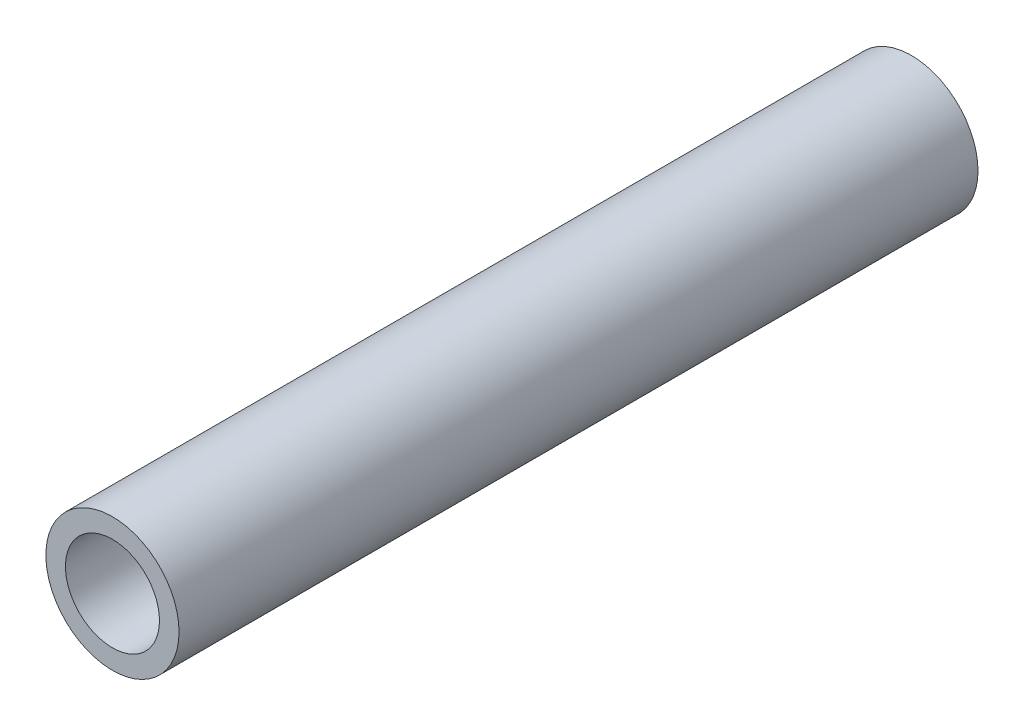
SolidWorks part; units mm, degrees
material "PVC Rigid"
ref_plane "Front Plane" through (0, 0, 0) normal (0, 0, 1) x (1, 0, 0)
ref_plane "Top Plane" through (0, 0, 0) normal (0, 1, 0) x (1, 0, 0)
ref_plane "Right Plane" through (0, 0, 0) normal (1, 0, 0) x (0, 0, -1)
sketch "Sketch1" plane through (0, 0, 0) normal (0, 0, 1) x (1, 0, 0)
  circle A0 centre (0, 0) radius 6.35
  circle A2 centre (0, 0) radius 4.4831
  dimension "D1" = 12.7
  dimension "D2" = 1.8669
extrude "Boss-Extrude1" add sketch "Sketch1" along normal blind 76.2
